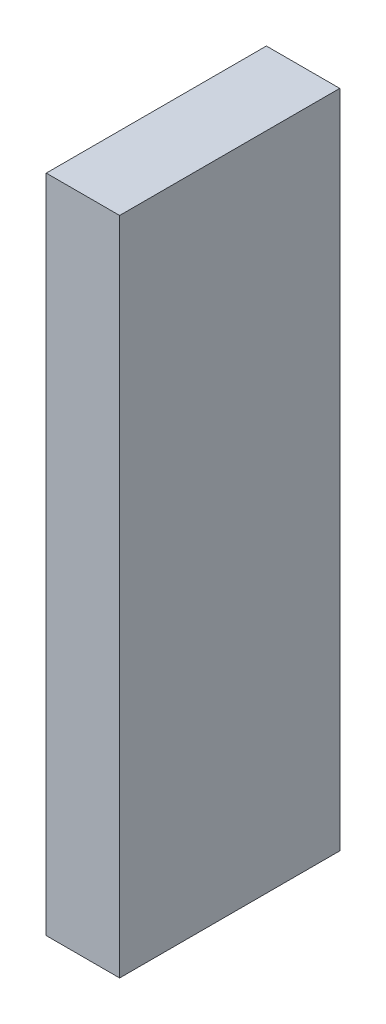
SolidWorks part; units mm, degrees
material "POLYURETHANE (11671)"
ref_plane "Front Plane" through (0, 0, 0) normal (0, 0, 1) x (1, 0, 0)
ref_plane "Top Plane" through (0, 0, 0) normal (0, 1, 0) x (1, 0, 0)
ref_plane "Right Plane" through (0, 0, 0) normal (1, 0, 0) x (0, 0, -1)
sketch "Sketch1" plane through (0, 0, 0) normal (1, 0, 0) x (0, 0, -1)
  line L1 (-4.7625, -14.2875) -> (4.7625, -14.2875)
  line L2 (-4.7625, -14.2875) -> (-4.7625, 14.2875)
  line L3 (-4.7625, 14.2875) -> (4.7625, 14.2875)
  line L4 (4.7625, -14.2875) -> (4.7625, 14.2875)
  line L5 (-4.7625, -14.2875) -> (4.7625, 14.2875) construction
  line L6 (-4.7625, 14.2875) -> (4.7625, -14.2875) construction
  point P0 (0, 0)
  dimension "D1" = 9.525
  dimension "D2" = 28.575
extrude "Boss-Extrude1" add sketch "Sketch1" along normal blind 3.175
